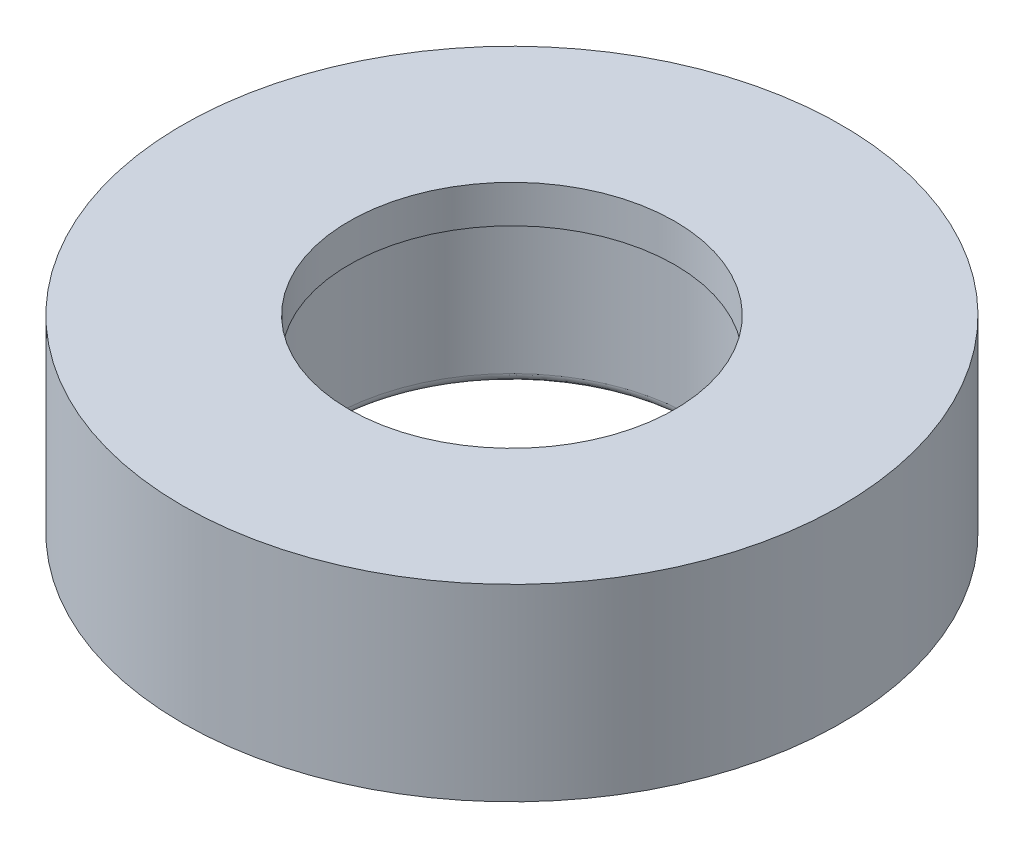
SolidWorks part; units mm, degrees
ref_plane "Спереди" through (0, 0, 0) normal (0, 0, 1) x (1, 0, 0)
ref_plane "Сверху" through (0, 0, 0) normal (0, 1, 0) x (1, 0, 0)
ref_plane "Справа" through (0, 0, 0) normal (1, 0, 0) x (0, 0, -1)
sketch "Эскиз1" plane through (0, 0, 0) normal (0, 1, 0) x (1, 0, 0)
  circle A0 centre (0, 0) radius 9.65
  circle A1 centre (0, 0) radius 17.5
  dimension "D1" = 19.3
  dimension "D2" = 35
extrude "Бобышка-Вытянуть1" add sketch "Эскиз1" along normal blind 10
sketch "Эскиз2" plane through (0, 10, 0) normal (0, 1, 0) x (1, 0, 0)
  circle A0 centre (0, 0) radius 9.65
  circle A1 centre (0, 0) radius 8.65
  dimension "D1" = 1
extrude "Бобышка-Вытянуть2" add sketch "Эскиз2" against normal blind 2
fillet "Скругление1" radius 0.5 1 edges at (0, 0, 9.65)
